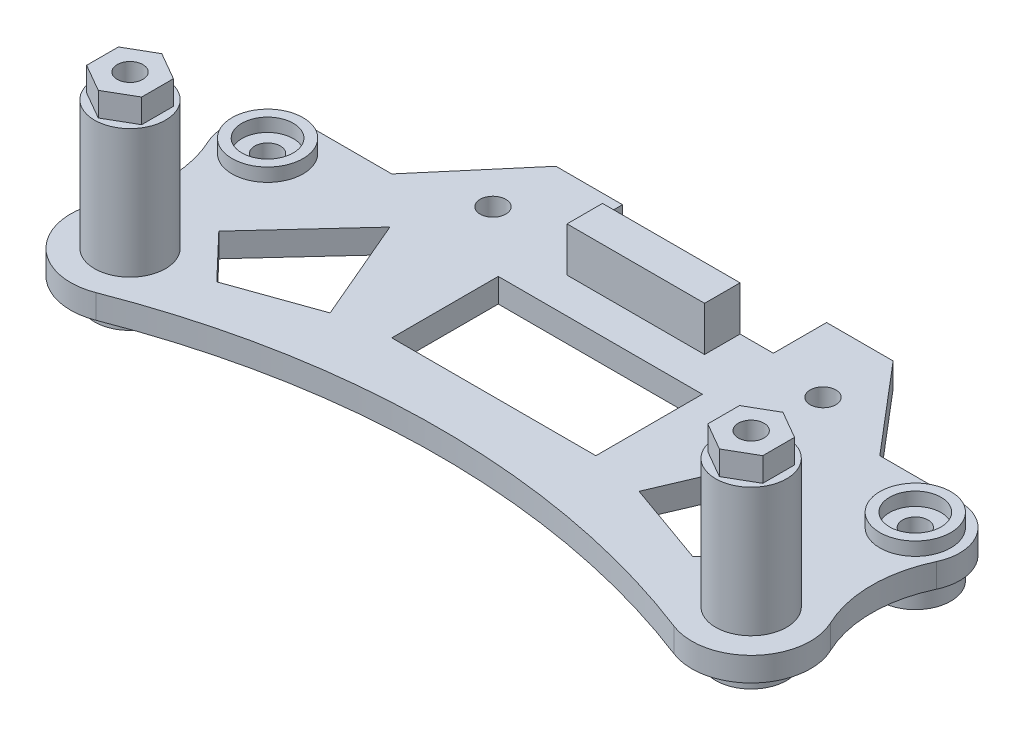
SolidWorks part; units mm, degrees
ref_plane "Front Plane" through (0, 0, 0) normal (0, 0, 1) x (1, 0, 0)
ref_plane "Top Plane" through (0, 0, 0) normal (0, 1, 0) x (1, 0, 0)
ref_plane "Right Plane" through (0, 0, 0) normal (1, 0, 0) x (0, 0, -1)
sketch "Sketch1" plane through (0, 0, 0) normal (0, 1, 0) x (1, 0, 0)
  line L0 (0, 0) -> (0, -22.963) construction
  line L2 (-39.5, 15.2679) -> (-36.5, 13.5359)
  line L3 (-36.5, 13.5359) -> (-33.5, 15.2679)
  line L4 (-33.5, 15.2679) -> (-33.5, 18.7321)
  line L5 (-33.5, 18.7321) -> (-36.5, 20.4641)
  line L6 (-36.5, 20.4641) -> (-39.5, 18.7321)
  line L7 (-39.5, 18.7321) -> (-39.5, 15.2679)
  line L8 (36.5, 20.4641) -> (33.5, 18.7321)
  line L9 (33.5, 18.7321) -> (33.5, 15.2679)
  line L10 (33.5, 15.2679) -> (36.5, 13.5359)
  line L11 (36.5, 13.5359) -> (39.5, 15.2679)
  line L12 (39.5, 15.2679) -> (39.5, 18.7321)
  line L13 (39.5, 18.7321) -> (36.5, 20.4641)
  circle A0 centre (-35, 0) radius 4
  circle A1 centre (35, 0) radius 4
  circle A2 centre (-35, 0) radius 2.1
  circle A3 centre (35, 0) radius 2.1
  circle A4 centre (-36.5, 17) radius 4
  circle A5 centre (36.5, 17) radius 4
  circle A6 centre (-36.5, 17) radius 3 construction
  circle A7 centre (36.5, 17) radius 3 construction
  circle A8 centre (-18.6, 24.5) radius 4.3
  circle A9 centre (18.6, 24.5) radius 4.3
  circle A10 centre (-18.6, 24.5) radius 2.9
  circle A11 centre (18.6, 24.5) radius 2.9
  dimension "D1" = 8
  dimension "D2" = 8
  dimension "D3" = 78
  dimension "D4" = 4.2
  dimension "D5" = 4.2
  dimension "D6" = 81
  dimension "D7" = 8
  dimension "D8" = 8
  dimension "D9" = 25
  dimension "D12" = 8.6
  dimension "D13" = 8.6
  dimension "D14" = 45.8
  dimension "D15" = 32.8
  dimension "D16" = 5.8
  dimension "D17" = 5.8
  dimension "D10" = 6
  dimension "D11" = 6
extrude "Boss-Extrude1" add sketch "Sketch1" against normal blind 2.5
sketch "Sketch2" plane through (0, 0, 0) normal (0, 1, 0) x (1, 0, 0)
  line L0 (-36.5, 22) -> (-27.5, 22)
  line L1 (36.5, 22) -> (27.5, 22)
  line L2 (-11.5, 26) -> (11.5, 26)
  line L3 (11.5, 26) -> (11.5, 32)
  line L4 (11.5, 32) -> (19, 32)
  line L5 (19, 32) -> (27.5, 22)
  line L6 (-11.5, 26) -> (-11.5, 32)
  line L7 (-11.5, 32) -> (-19, 32)
  line L8 (-19, 32) -> (-27.5, 22)
  line L9 (0, 0) -> (0, 8.0188) construction
  line L10 (-17.4089, 4.9582) -> (-22.4243, 16.7115)
  line L11 (-11.5, 18) -> (11.5, 18)
  line L12 (-11.5, 18) -> (-11.5, 6)
  line L13 (-11.5, 6) -> (11.5, 6)
  line L14 (11.5, 18) -> (11.5, 6)
  line L15 (-22.4243, 16.7115) -> (-31.6642, 6.6693)
  line L16 (-31.6642, 6.6693) -> (-26.8304, 1.6063)
  line L17 (-26.8304, 1.6063) -> (-17.4089, 4.9582)
  line L18 (31.6642, 6.6693) -> (26.8304, 1.6063)
  line L19 (22.4243, 16.7115) -> (31.6642, 6.6693)
  line L20 (17.4089, 4.9582) -> (22.4243, 16.7115)
  line L21 (26.8304, 1.6063) -> (17.4089, 4.9582)
  arc A0 (-41.0488, 2.8814) -> (-32.575, -6.2457) centre (-35, 0) ccw
  arc A1 (32.575, -6.2457) -> (41.0488, 2.8814) centre (35, 0) ccw
  arc A2 (-41.0231, 14.869) -> (-36.5, 22) centre (-36.5, 17) cw
  arc A3 (41.0231, 14.869) -> (36.5, 22) centre (36.5, 17) ccw
  circle A4 centre (35, 0) radius 4 construction
  circle A5 centre (-35, 0) radius 4 construction
  arc A6 (-32.575, -6.2457) -> (32.575, -6.2457) centre (0, -90.1437) cw
  arc A7 (-41.0488, 2.8814) -> (-41.0231, 14.869) centre (-53.688, 8.9022) ccw
  circle A8 centre (-36.5, 17) radius 4 construction
  arc A9 (41.0488, 2.8814) -> (41.0231, 14.869) centre (53.688, 8.9022) cw
  circle A10 centre (36.5, 17) radius 4 construction
  circle A11 centre (-36.5, 17) radius 1.45
  circle A12 centre (-35, 0) radius 2.25
  circle A13 centre (35, 0) radius 2.25
  circle A14 centre (36.5, 17) radius 1.45
  circle A15 centre (18.6, 24.5) radius 1.45
  circle A16 centre (-18.6, 24.5) radius 1.45
  dimension "D1" = 2.7
  dimension "D2" = 2.7
  dimension "D3" = 90
  dimension "D4" = 1
  dimension "D5" = 1
  dimension "D6" = 14
  dimension "D7" = 14
  dimension "D8" = 23
  dimension "D22" = 2.9
  dimension "D23" = 2.9
  dimension "D24" = 2.9
  dimension "D25" = 2.9
  dimension "D26" = 4.5
  dimension "D27" = 4.5
  dimension "D9" = 6
  dimension "D10" = 10
  dimension "D11" = 7.5
  dimension "D12" = 7.5
  dimension "D13" = 9
  dimension "D14" = 9
  dimension "D15" = 23
  dimension "D16" = 12
  dimension "D17" = 8
  dimension "D18" = 6
  dimension "D19" = 11
  dimension "D20" = 7
  dimension "D21" = 10
extrude "Boss-Extrude2" add sketch "Sketch2" along normal blind 2.7
sketch "Sketch3" plane through (0, 2.7, 0) normal (0, 1, 0) x (1, 0, 0)
  line L0 (11.5, 26) -> (-11.5, 26) construction
  line L1 (-7.75, 26) -> (7.75, 26)
  line L2 (-7.75, 26) -> (-7.75, 22)
  line L3 (-7.75, 22) -> (7.75, 22)
  line L4 (7.75, 26) -> (7.75, 22)
  line L5 (0, -0.1437) -> (0, 13.4224) construction
  arc A0 (32.575, -6.2457) -> (-32.575, -6.2457) centre (0, -90.1437) ccw construction
  dimension "D1" = 15.5
  dimension "D2" = 4
extrude "Boss-Extrude3" add sketch "Sketch3" along normal blind 5
sketch "Sketch4" plane through (0, 2.7, 0) normal (0, 1, 0) x (1, 0, 0)
  circle A0 centre (-36.5, 17) radius 4
  circle A1 centre (-36.5, 17) radius 2.9
  circle A2 centre (36.5, 17) radius 2.9
  circle A3 centre (36.5, 17) radius 4
  dimension "D1" = 8
  dimension "D2" = 8
  dimension "D3" = 5.8
  dimension "D4" = 5.8
extrude "Boss-Extrude4" add sketch "Sketch4" along normal blind 1.5
sketch "Sketch5" plane through (0, 2.7, 0) normal (0, 1, 0) x (1, 0, 0)
  circle A0 centre (-35, 0) radius 4
  circle A1 centre (-35, 0) radius 2.1
  circle A2 centre (35, 0) radius 4
  circle A3 centre (35, 0) radius 2.1
  dimension "D1" = 8
  dimension "D2" = 4.2
  dimension "D3" = 8
  dimension "D4" = 4.2
extrude "Boss-Extrude5" add sketch "Sketch5" along normal blind 14.5
sketch "Sketch6" plane through (0, 17.2, 0) normal (0, 1, 0) x (1, 0, 0)
  line L1 (-35, 3.5796) -> (-38.1, 1.7898)
  line L2 (-38.1, 1.7898) -> (-38.1, -1.7898)
  line L3 (-38.1, -1.7898) -> (-35, -3.5796)
  line L4 (-35, -3.5796) -> (-31.9, -1.7898)
  line L5 (-31.9, -1.7898) -> (-31.9, 1.7898)
  line L6 (-31.9, 1.7898) -> (-35, 3.5796)
  line L7 (31.9, 1.7898) -> (31.9, -1.7898)
  line L8 (31.9, -1.7898) -> (35, -3.5796)
  line L9 (35, -3.5796) -> (38.1, -1.7898)
  line L10 (38.1, -1.7898) -> (38.1, 1.7898)
  line L11 (38.1, 1.7898) -> (35, 3.5796)
  line L12 (35, 3.5796) -> (31.9, 1.7898)
  circle A0 centre (-35, 0) radius 3.1 construction
  circle A1 centre (35, 0) radius 3.1 construction
  circle A2 centre (-35, 0) radius 1.45
  circle A3 centre (35, 0) radius 1.45
  dimension "D3" = 2.9
  dimension "D4" = 2.9
  dimension "D1" = 6.2
  dimension "D2" = 6.2
extrude "Boss-Extrude6" add sketch "Sketch6" along normal blind 2.7
